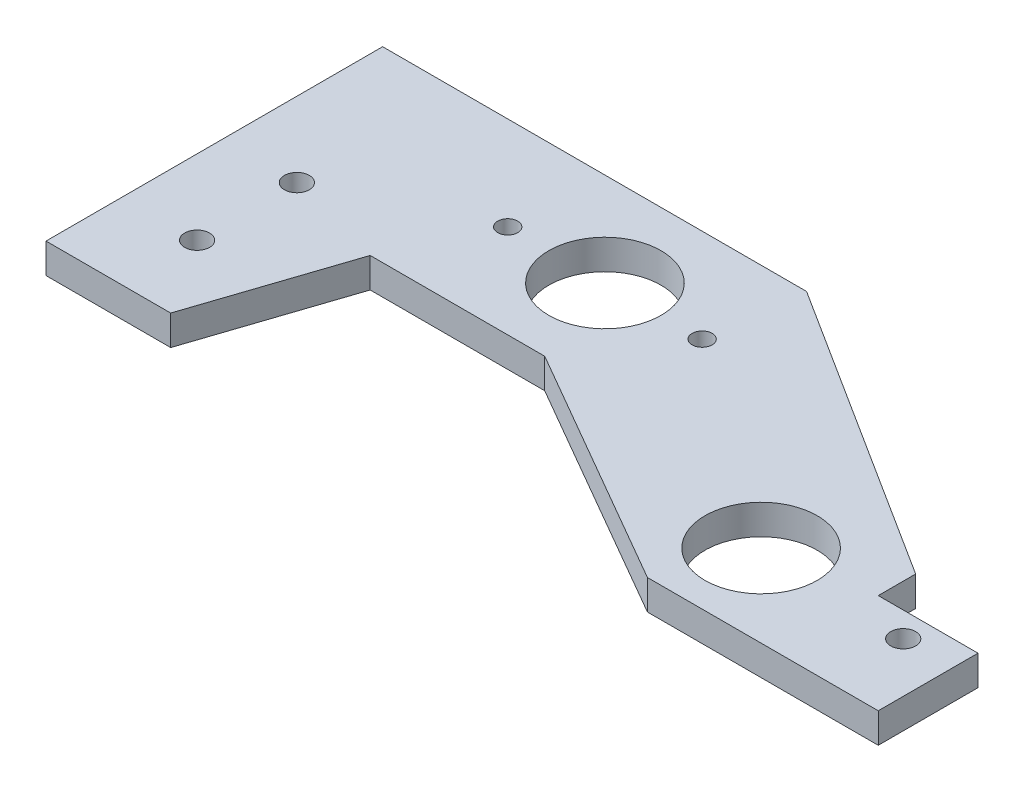
SolidWorks part; units mm, degrees
ref_plane "Front Plane" through (0, 0, 0) normal (0, 0, 1) x (1, 0, 0)
ref_plane "Top Plane" through (0, 0, 0) normal (0, 1, 0) x (1, 0, 0)
ref_plane "Right Plane" through (0, 0, 0) normal (1, 0, 0) x (0, 0, -1)
sketch "Sketch1" plane through (0, 0, 0) normal (0, 1, 0) x (1, 0, 0)
  line L0 (-76.2, 14.7491) -> (-14.3313, -20.9708)
  line L1 (25.4, 13.9542) -> (-50.8, 62.3741)
  line L2 (25.4, 13.9542) -> (25.4, -20.9708)
  line L3 (-50.8, 62.3741) -> (-152.4, 62.3741)
  line L4 (-152.4, 62.3741) -> (-152.4, 14.7491)
  line L5 (-152.4, 14.7491) -> (-76.2, 14.7491)
  line L6 (-14.3313, -20.9708) -> (25.4, -20.9708)
  circle A0 centre (0, 0) radius 14.2875
  circle A1 centre (0, 0) radius 23.8125 construction
  circle A3 centre (0, 0) radius 25.4 construction
  dimension "D1" = 28.575
  dimension "D2" = 47.625
  dimension "D3" = 50.8
  dimension "D4" = 150
  dimension "D5" = 34.925
  dimension "D6" = 76.2
  dimension "D7" = 152.4
  dimension "D8" = 101.6
  dimension "D9" = 47.625
extrude "Boss-Extrude1" add sketch "Sketch1" along normal blind 7.62
sketch "Sketch2" plane through (0, 7.62, 0) normal (0, 1, 0) x (1, 0, 0)
  line L0 (-152.4, 38.5616) -> (-44.1395, 38.5616) construction
  line L1 (-152.4, 62.3741) -> (-152.4, 14.7491) construction
  circle A0 centre (-78.3356, 38.5616) radius 14.2875
  circle A1 centre (-78.3356, 38.5616) radius 24.7523 construction
  circle A2 centre (-103.0879, 38.5616) radius 2.5527
  circle A3 centre (-53.5833, 38.5616) radius 2.5527
  circle A4 centre (0, 0) radius 14.2875 construction
  circle A5 centre (0, 0) radius 14.2875 construction
  point P10 (-78.3356, 38.5616)
  dimension "D1" = 2
  dimension "D2" = 49.5046
  dimension "D3" = 28.575
  dimension "D5" = 5.1054
  dimension "D4" = 87.3125
extrude "Cut-Extrude1" cut sketch "Sketch2" against normal through all
sketch "Sketch5" plane through (0, 7.62, 0) normal (0, 1, 0) x (1, 0, 0)
  line L0 (25.4, -20.9708) -> (50.8, -20.9708)
  line L1 (50.8, -20.9708) -> (50.8, 4.4292)
  line L2 (50.8, 4.4292) -> (25.4, 4.4292)
  line L3 (25.4, -20.9708) -> (25.4, 13.9542) construction
  line L4 (25.4, 4.4292) -> (25.4, -20.9708)
  circle A0 centre (38.1, -1.9208) radius 3.175
  dimension "D3" = 12.7
  dimension "D5" = 6.35
  dimension "D1" = 25.4
  dimension "D2" = 25.4
  dimension "D4" = 19.05
extrude "Boss-Extrude3" add sketch "Sketch5" against normal up to surface (7.62 mm away) up to face at (-53.5833, 0, -36.0089)
sketch "Sketch6" plane through (0, 7.62, 0) normal (0, 1, 0) x (1, 0, 0)
  line L0 (-152.4, -23.3509) -> (-127, -23.3509)
  line L1 (-152.4, 14.7491) -> (-76.2, 14.7491) construction
  line L2 (-152.4, -23.3509) -> (-152.4, 14.7491) construction
  line L3 (-152.4, -23.3509) -> (-158.75, -23.3509)
  line L4 (-158.75, -23.3509) -> (-158.75, 62.3741)
  line L5 (-158.75, 62.3741) -> (-152.4, 62.3741)
  line L6 (-50.8, 62.3741) -> (-152.4, 62.3741) construction
  line L7 (-152.4, 62.3741) -> (-152.4, 14.7491) construction
  line L8 (-127, -23.3509) -> (-114.3, 14.7491)
  line L9 (-152.4, 62.3741) -> (-152.4, 14.7491)
  line L10 (-152.4, 14.7491) -> (-114.3, 14.7491)
  dimension "D1" = 6.35
  dimension "D2" = 38.1
  dimension "D3" = 25.4
extrude "Boss-Extrude4" add sketch "Sketch6" against normal up to surface (7.62 mm away) up to face at (-53.5833, 0, -36.0089)
sketch "Sketch7" plane through (0, 7.62, 0) normal (0, 1, 0) x (1, 0, 0)
  line L0 (-139.7, 62.3741) -> (-139.7, -23.3509) construction
  line L4 (-50.8, 62.3741) -> (-158.75, 62.3741) construction
  line L5 (-158.75, -23.3509) -> (-127, -23.3509) construction
  line L6 (-158.75, 62.3741) -> (-158.75, -23.3509) construction
  circle A0 centre (-139.7, 21.4801) radius 3.175
  circle A1 centre (-139.7, -3.9199) radius 3.175
  dimension "D1" = 40.894
  dimension "D3" = 6.35
  dimension "D10" = 6.35
  dimension "D2" = 25.4
  dimension "D4" = 19.05
extrude "Cut-Extrude2" cut sketch "Sketch7" against normal through all
sketch "Sketch10" plane through (0, 7.62, 0) normal (0, 1, 0) x (1, 0, 0)
  line L0 (-76.2, 14.7491) -> (-69.85, 14.7491)
  line L1 (-14.3313, -20.9708) -> (50.8, -20.9708) construction
  line L2 (-69.85, 14.7491) -> (-7.9813, -20.9708)
  line L4 (-76.2, 14.7491) -> (-14.3313, -20.9708) construction
  line L5 (-76.2, 14.7491) -> (-14.3313, -20.9708)
  line L6 (-14.3313, -20.9708) -> (-7.9813, -20.9708)
  dimension "D1" = 3.175
extrude "Cut-Extrude3" cut sketch "Sketch10" against normal up to surface (7.62 mm away) up to face at (-139.7, 0, 0.7449)
